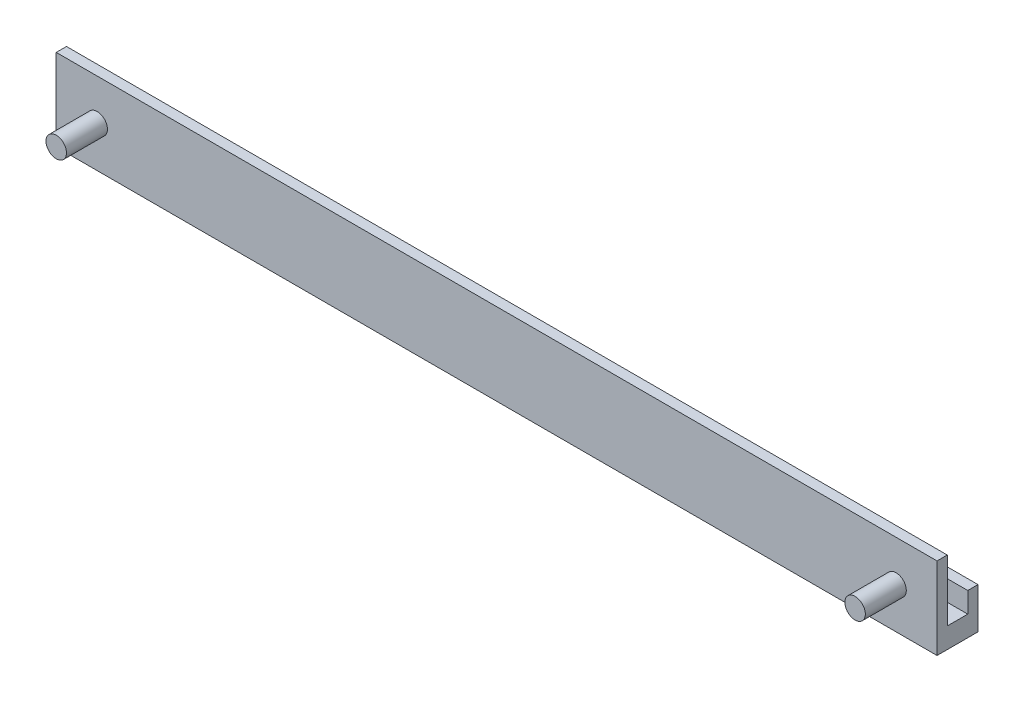
SolidWorks part; units mm, degrees
ref_plane "Front Plane" through (0, 0, 0) normal (0, 0, 1) x (1, 0, 0)
ref_plane "Top Plane" through (0, 0, 0) normal (0, 1, 0) x (1, 0, 0)
ref_plane "Right Plane" through (0, 0, 0) normal (1, 0, 0) x (0, 0, -1)
sketch "Sketch1" plane through (0, 0, 0) normal (0, 1, 0) x (1, 0, 0)
  line L1 (-107.5, 5) -> (107.5, 5)
  line L2 (-107.5, 5) -> (-107.5, -5)
  line L3 (-107.5, -5) -> (107.5, -5)
  line L4 (107.5, 5) -> (107.5, -5)
  line L5 (-107.5, 5) -> (107.5, -5) construction
  line L6 (-107.5, -5) -> (107.5, 5) construction
  point P0 (0, 0)
  dimension "D1" = 10
  dimension "D2" = 215
extrude "Boss-Extrude1" add sketch "Sketch1" along normal blind 5
sketch "Sketch4" plane through (0, 5, 0) normal (0, 1, 0) x (1, 0, 0)
  line L0 (-107.5, 5) -> (-107.5, -5) construction
  line L1 (-107.5, -2.5) -> (107.5, -2.5)
  line L2 (-107.5, -2.5) -> (-107.5, -5)
  line L3 (-107.5, -5) -> (107.5, -5)
  line L4 (107.5, -2.5) -> (107.5, -5)
  line L5 (-107.5, -5) -> (107.5, -5) construction
  line L6 (107.5, -5) -> (107.5, 5) construction
  dimension "D1" = 2.5
extrude "Boss-Extrude7" add sketch "Sketch4" along normal blind 15
sketch "Sketch6" plane through (0, 5, 0) normal (0, 1, 0) x (1, 0, 0)
  line L0 (-107.5, 5) -> (-107.5, -2.5) construction
  line L1 (-107.5, 2.5) -> (107.5, 2.5)
  line L2 (-107.5, 2.5) -> (-107.5, 5)
  line L3 (-107.5, 5) -> (107.5, 5)
  line L4 (107.5, 2.5) -> (107.5, 5)
  line L5 (107.5, -2.5) -> (107.5, 5) construction
  line L6 (107.5, 5) -> (-107.5, 5) construction
  dimension "D1" = 2.5
extrude "Boss-Extrude8" add sketch "Sketch6" along normal blind 5
sketch "Sketch7" plane through (0, 0, 5) normal (0, 0, 1) x (1, 0, 0)
  line L0 (-97.5, 20) -> (-97.5, 0) construction
  line L1 (-107.5, 20) -> (107.5, 20) construction
  line L2 (-107.5, 0) -> (107.5, 0) construction
  line L3 (-107.5, 20) -> (-107.5, 0) construction
  line L4 (97.5, 20) -> (97.5, 0) construction
  line L5 (107.5, 20) -> (107.5, 0) construction
  circle A0 centre (-97.5, 10) radius 2.5
  circle A1 centre (97.5, 10) radius 2.5
  point P8 (-107.5, 10)
  point P15 (107.5, 10)
  dimension "D1" = 5
  dimension "D3" = 5
  dimension "D2" = 10
  dimension "D4" = 10
extrude "Boss-Extrude9" add sketch "Sketch7" along normal blind 10
